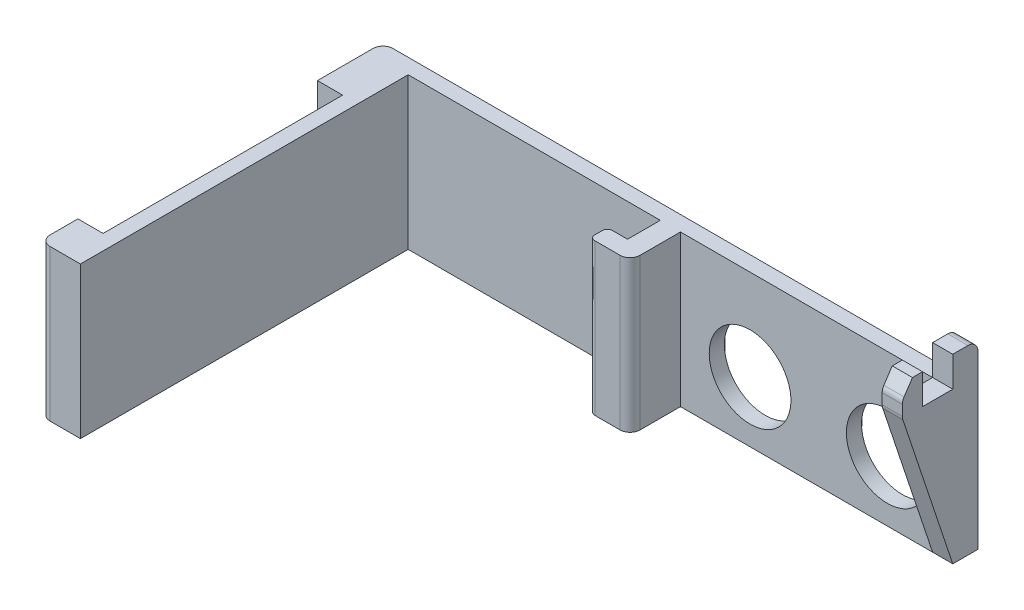
SolidWorks part; units mm, degrees
ref_plane "Front Plane" through (0, 0, 0) normal (0, 0, 1) x (1, 0, 0)
ref_plane "Top Plane" through (0, 0, 0) normal (0, 1, 0) x (1, 0, 0)
ref_plane "Right Plane" through (0, 0, 0) normal (1, 0, 0) x (0, 0, -1)
sketch "Sketch1" plane through (0, 0, 0) normal (0, 1, 0) x (1, 0, 0)
  line L0 (0, 0) -> (0, -10)
  line L1 (0, 0) -> (62, 0)
  line L2 (0, 0) -> (0, 3)
  line L5 (0, 0) -> (8, 0)
  line L7 (2, -65) -> (8, -65)
  line L8 (8, 0) -> (8, -65)
  line L9 (62, 0) -> (58, 0)
  line L10 (62, 0) -> (62, -8)
  line L11 (60, -10) -> (58, -10)
  line L12 (58, 0) -> (58, -10)
  line L25 (58, -10) -> (55, -10)
  line L26 (58, -10) -> (58, -6.5)
  line L27 (58, -6.5) -> (55, -6.5)
  line L28 (54, -9) -> (54, -7.5)
  line L29 (0, -10) -> (5, -10)
  line L30 (5, -10) -> (5, -57.5)
  line L31 (5, -57.5) -> (0, -57.5)
  line L32 (0, -57.5) -> (0, -63)
  line L33 (2, 5) -> (116, 5)
  line L34 (116, 5) -> (116, 0)
  line L35 (116, 0) -> (62, 0)
  line L36 (2, 5) -> (0, 5)
  line L37 (0, 5) -> (0, 3)
  arc A3 (62, -8) -> (60, -10) centre (60, -8) cw
  arc A4 (0, -63) -> (2, -65) centre (2, -63) ccw
  arc A6 (55, -6.5) -> (54, -7.5) centre (55, -7.5) ccw
  arc A7 (55, -10) -> (54, -9) centre (55, -9) cw
  point P20 (54, -6.5)
  point P26 (54, -10)
  dimension "D13" = 1
  dimension "D9" = 62
  dimension "D2" = 54
  dimension "D3" = 10
  dimension "D4" = 47.5
  dimension "D5" = 5
  dimension "D6" = 4
  dimension "D7" = 65
  dimension "D8" = 10
  dimension "D10" = 5
  dimension "D11" = 4
  dimension "D12" = 3.5
extrude "Boss-Extrude1" add sketch "Sketch1" along normal blind 30
sketch "Sketch2" plane through (0, 0, 0) normal (-1, 0, 0) x (0, 0, 1)
  line L0 (10, 30) -> (10, 0) construction
  line L1 (10, 12.5) -> (7.5, 12.5)
  line L2 (10, 12.5) -> (10, 17.5)
  line L3 (10, 17.5) -> (7.5, 17.5)
  line L4 (7.5, 12.5) -> (7.5, 17.5)
  line L5 (57.5, 30) -> (57.5, 0) construction
  line L6 (57.5, 12.5) -> (60, 12.5)
  line L7 (57.5, 12.5) -> (57.5, 17.5)
  line L8 (57.5, 17.5) -> (60, 17.5)
  line L9 (60, 12.5) -> (60, 17.5)
  line L10 (-5, 0) -> (10, 0) construction
  line L11 (-5, 30) -> (10, 30) construction
  line L12 (57.5, 0) -> (63, 0) construction
  point P12 (8.75, 12.5)
  dimension "D1" = 5
  dimension "D2" = 2.5
  dimension "D3" = 12.5
  dimension "D4" = 12.5
  dimension "D5" = 12.5
  dimension "D6" = 5
  dimension "D7" = 2.5
extrude "Cut-Extrude1" cut sketch "Sketch2" against normal blind 5
sketch "Sketch3" plane through (0, 0, -5) normal (0, 0, -1) x (-1, 0, 0)
  line L0 (0, 0) -> (-116, 0) construction
  line L1 (-116, 30) -> (-116, 0) construction
  circle A0 centre (-103, 12) radius 8.1
  circle A1 centre (-75.8, 12) radius 8.1
  dimension "D1" = 16.2
  dimension "D2" = 12
  dimension "D3" = 16.2
  dimension "D4" = 12
  dimension "D5" = 27.2
  dimension "D6" = 13
extrude "Cut-Extrude2" cut sketch "Sketch3" against normal through all
sketch "Sketch4" plane through (0, 0, -5) normal (0, 0, -1) x (-1, 0, 0)
  line L0 (0, 0) -> (-116, 0) construction
  line L1 (-91, 18) -> (-87.8, 18)
  line L2 (-93, 16) -> (-93, 10)
  line L3 (-91, 8) -> (-87.8, 8)
  line L4 (-85.8, 16) -> (-85.8, 10)
  line L5 (0, 30) -> (-116, 30) construction
  circle A0 centre (-75.8, 12) radius 8.1 construction
  circle A1 centre (-103, 12) radius 8.1 construction
  arc A2 (-93, 10) -> (-91, 8) centre (-91, 10) ccw
  arc A3 (-87.8, 8) -> (-85.8, 10) centre (-87.8, 10) ccw
  arc A4 (-87.8, 18) -> (-85.8, 16) centre (-87.8, 16) cw
  arc A5 (-91, 18) -> (-93, 16) centre (-91, 16) ccw
  dimension "D5" = 2
  dimension "D1" = 10
  dimension "D2" = 10
  dimension "D3" = 8
  dimension "D4" = 12
extrude "Boss-Extrude2" [suppressed] add sketch "Sketch4" along normal blind 2.6
sketch "Sketch8" plane through (116, 0, 0) normal (1, 0, 0) x (0, 0, -1)
  line L0 (0, 0) -> (0, 30)
  line L1 (0, 30) -> (-6, 30)
  line L2 (-6, 30) -> (-6, 36)
  line L3 (-6, 36) -> (-8, 36)
  line L6 (5, 30) -> (0, 30)
  line L7 (5, 30) -> (5, 34)
  line L8 (3, 36) -> (0, 36)
  line L9 (0, 30) -> (0, 36)
  line L10 (-9.8974, 29.6921) -> (0, 0)
  line L11 (-8, 36) -> (-9.6641, 33.5038)
  line L12 (-10, 32.3944) -> (-10, 30.3246)
  arc A0 (5, 34) -> (3, 36) centre (3, 34) ccw
  arc A1 (-10, 30.3246) -> (-9.8974, 29.6921) centre (-8, 30.3246) ccw
  arc A2 (-9.6641, 33.5038) -> (-10, 32.3944) centre (-8, 32.3944) ccw
  point P12 (-7, 36)
  point P18 (-10, 30)
  point P21 (-10, 33)
  line M18 (5, 30) -> (0, 30)
  line M19 (0, 30) -> (0, 0)
  dimension "D8" = 2
  dimension "D9" = 2
  dimension "D1" = 6
  dimension "D2" = 6
  dimension "D3" = 6
  dimension "D4" = 3
  dimension "D5" = 2
  dimension "D6" = 4
  dimension "D7" = 3
extrude "Boss-Extrude5" add sketch "Sketch8" against normal blind 4 contours L11 A2 L12 A1 L10 L1 L2 L3 M19 | L7 A0 L8 L9 M18
sketch "Sketch10" plane through (0, 0, -5) normal (0, 0, -1) x (-1, 0, 0)
  line L0 (0, 30) -> (-112, 30) construction
  line L1 (-112, 30) -> (-65.8, 30)
  line L2 (-113, 25) -> (-113, 1.5)
  line L3 (-113, 1.5) -> (-65.8, 1.5)
  line L4 (-65.8, 30) -> (-65.8, 1.5)
  line L5 (-113, 25) -> (-112, 30)
  line L6 (-91, 18) -> (-87.8, 18)
  line L7 (-93, 16) -> (-93, 10)
  line L8 (-91, 8) -> (-87.8, 8)
  line L9 (-85.8, 16) -> (-85.8, 10)
  line L11 (-65.8, 30) -> (0, 30)
  line L12 (-65.8, 30) -> (-65.8, 26)
  line L13 (-65.8, 26) -> (0, 26)
  line L14 (0, 30) -> (0, 26)
  circle A0 centre (-103, 12) radius 8.1 construction
  circle A1 centre (-75.8, 12) radius 8.1 construction
  arc A2 (-87.8, 8) -> (-85.8, 10) centre (-87.8, 10) ccw
  arc A3 (-93, 10) -> (-91, 8) centre (-91, 10) ccw
  arc A4 (-91, 18) -> (-93, 16) centre (-91, 16) ccw
  arc A5 (-87.8, 18) -> (-85.8, 16) centre (-87.8, 16) cw
  point P0 (-113, 30)
  dimension "D6" = 2
  dimension "D1" = 10
  dimension "D2" = 10.5
  dimension "D3" = 10
  dimension "D4" = 47.2
  dimension "D5" = 0
  dimension "D7" = 5
  dimension "D8" = 1
  dimension "D9" = 4
extrude "Cut-Extrude3" cut sketch "Sketch10" against normal blind 2
fillet "Fillet1" radius 2 2 edges at (0, 28, -3) (0, 13, -5)
sketch "Sketch7" [suppressed] plane through (0, 0, -7.6) normal (0, 0, -1) x (-1, 0, 0)
  line L0 (-91.375, 8.55) -> (-91.375, 0.15)
  line L1 (-91.375, 0.15) -> (-90, 0.15)
  line L2 (-90, 0.15) -> (-90, 7.95)
  line L3 (-90, 7.95) -> (-89.85, 7.95)
  line L4 (-89.85, 7.95) -> (-89.85, 0.15)
  line L5 (-89.85, 0.15) -> (-88.475, 0.15)
  line L6 (-88.475, 0.15) -> (-88.475, 7.95)
  line L7 (-88.475, 7.95) -> (-88.325, 7.95)
  line L8 (-88.325, 7.95) -> (-88.325, 0.15)
  line L9 (-88.325, 0.15) -> (-86.95, 0.15)
  line L10 (-86.95, 0.15) -> (-86.95, 7.95)
  line L11 (-86.95, 7.95) -> (-86.8, 7.95)
  line L12 (-86.8, 7.95) -> (-86.8, 0.15)
  line L13 (-86.8, 0.15) -> (-85.425, 0.15)
  line L14 (-85.425, 0.15) -> (-85.425, 8.55)
  line L15 (-85.425, 8.55) -> (-85.275, 8.7)
  line L16 (-85.275, 8.7) -> (-85.275, 0.1469)
  line L17 (-85.275, 0.1469) -> (-85.275, 0)
  line L18 (-2, 0) -> (-114, 0) construction
  line L19 (-91.375, 8.55) -> (-91.525, 8.7)
  line L20 (-91.525, 8.7) -> (-91.525, 0)
  line L21 (-91.525, 0) -> (-85.275, 0)
  point P2 (-90.6875, 0.15)
  point P24 (0, 0)
  point P25 (0, 0)
  dimension "D1" = 0.15
  dimension "D2" = 0.15
  dimension "D3" = 0.15
  dimension "D4" = 0.15
  dimension "D5" = 0.15
  dimension "D6" = 0.15
  dimension "D7" = 0.15
  dimension "D8" = 7.8
  dimension "D9" = 7.8
  dimension "D10" = 7.8
  dimension "D11" = 0.15
  dimension "D12" = 8.7
  dimension "D13" = 0
  dimension "D14" = 0
  dimension "D15" = 1.375
  dimension "D16" = 1.375
  dimension "D17" = 1.375
  dimension "D18" = 1.375
  dimension "D19" = 8.55
  dimension "D20" = 8.55
  dimension "D21" = 8.7
extrude "Boss-Extrude4" [suppressed] add sketch "Sketch7" against normal blind 2.35
equation "\"2.5.00mm\"=7"
